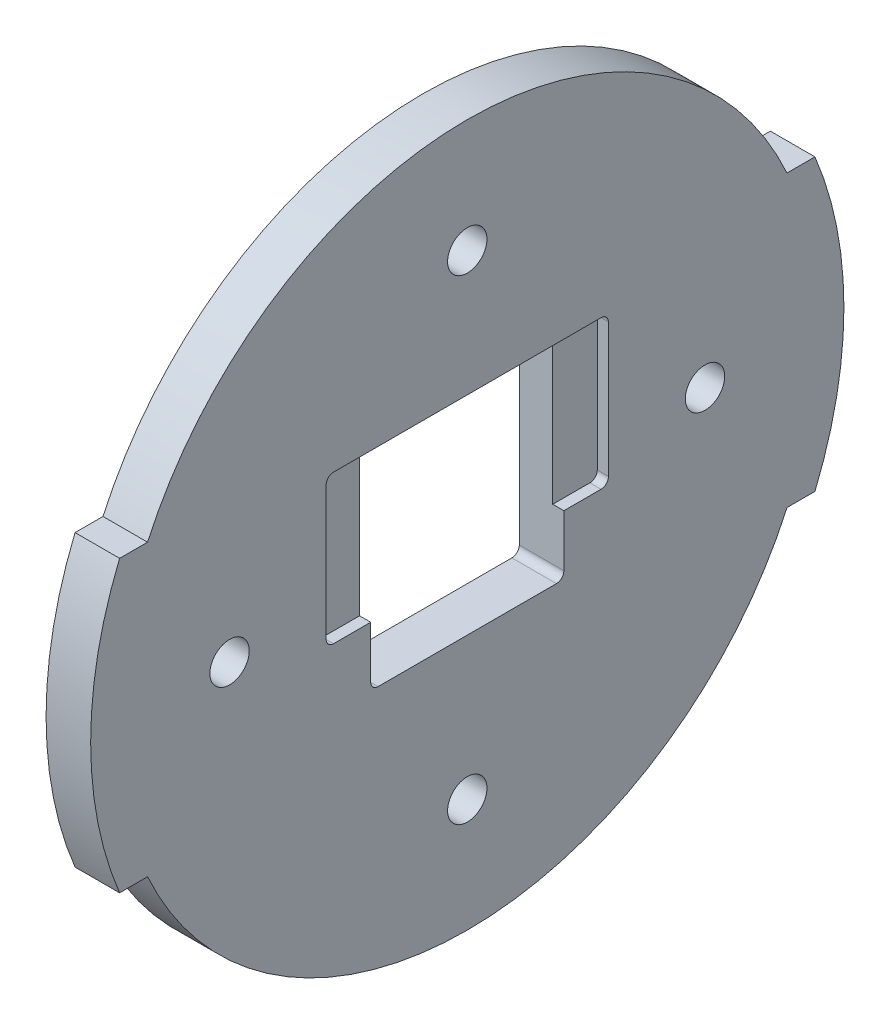
SolidWorks part; units mm, degrees
material "Perspex (TM) GS Acrylic Cast Sheet"
ref_plane "Front Plane" through (0, 0, 0) normal (0, 0, 1) x (1, 0, 0)
ref_plane "Top Plane" through (0, 0, 0) normal (0, 1, 0) x (1, 0, 0)
ref_plane "Right Plane" through (0, 0, 0) normal (1, 0, 0) x (0, 0, -1)
sketch "Sketch1" plane through (0, 0, 0) normal (1, 0, 0) x (0, 0, -1)
  line L0 (-46.8, 19.5) -> (-43.0385, 19.5)
  line L3 (-46.8, -19.5) -> (-43.0385, -19.5)
  line L4 (46.8, -19.5) -> (43.0385, -19.5)
  line L5 (46.8, 19.5) -> (43.0385, 19.5)
  arc A0 (-43.0385, -19.5) -> (43.0385, -19.5) centre (0, 0) ccw
  arc A1 (-46.8, 19.5) -> (-46.8, -19.5) centre (0, 0) ccw
  arc A2 (46.8, -19.5) -> (46.8, 19.5) centre (0, 0) ccw
  arc A3 (43.0385, 19.5) -> (-43.0385, 19.5) centre (0, 0) ccw
  dimension "D1" = 101.4
  dimension "D2" = 94.5
  dimension "D3" = 19.5
  dimension "D4" = 39
  dimension "D5" = 19.5
  dimension "D6" = 39
extrude "Boss-Extrude1" add sketch "Sketch1" along normal blind 6
sketch "Sketch2" plane through (6, 0, 0) normal (1, 0, 0) x (0, 0, -1)
  line L0 (12, -12.85) -> (-12, -12.85)
  line L1 (13, -3.85) -> (13, -11.85)
  line L2 (12, -11.85) -> (-12, -11.85)
  line L3 (-13, -11.85) -> (-13, -3.85)
  line L4 (-13, -3.85) -> (-13, 14.15)
  line L5 (13, -3.85) -> (13, 14.15)
  line L6 (12, 15.15) -> (-12, 15.15)
  line L7 (12, -12.85) -> (-12, -12.85) construction
  arc A0 (-13, -11.85) -> (-12, -12.85) centre (-12, -11.85) ccw
  arc A1 (13, -11.85) -> (12, -12.85) centre (12, -11.85) cw
  arc A4 (12, -11.85) -> (13, -10.85) centre (12, -10.85) ccw
  arc A5 (-13, -10.85) -> (-12, -11.85) centre (-12, -10.85) ccw
  arc A8 (-13, 14.15) -> (-12, 15.15) centre (-12, 14.15) cw
  arc A9 (13, 14.15) -> (12, 15.15) centre (12, 14.15) ccw
  point P26 (13, 15.15)
  dimension "D2" = 1
  dimension "D4" = 1
  dimension "D1" = 19
  dimension "D3" = 1
extrude "Cut-Extrude1" cut sketch "Sketch2" against normal blind 20 contours L5 A9 L6 A8 L4 L3 A5 L2 A4 L1 | A5 L3 A0 L0 A1 L1 A4 L2
sketch "Sketch3" plane through (6, 0, 0) normal (1, 0, 0) x (0, 0, -1)
  line L0 (0, 0) -> (-33.4108, 33.4108)
  line L1 (-33.4108, 33.4108) -> (33.4108, -33.4108)
  line L2 (0, 0) -> (33.4108, 33.4108)
  line L3 (0, 0) -> (-33.4108, -33.4108)
  circle A0 centre (0, 0) radius 47.25 construction
ref_plane "Plane1" through (0, 33.4108, 33.4108) normal (0, 0.7071, 0.7071) x (-1, 0, 0)
ref_plane "Plane2" through (0, -33.4108, 33.4108) normal (0, -0.7071, 0.7071) x (-1, 0, 0)
ref_plane "Plane3" through (0, 33.4108, -33.4108) normal (0, 0.7071, -0.7071) x (-1, 0, 0)
ref_plane "Plane4" through (0, -33.4108, -33.4108) normal (0, -0.7071, -0.7071) x (-1, 0, 0)
hole_wizard "M5 Clearance Hole1" positions "Sketch15" profile "Sketch14" hole size "M5" standard "ISO"
sketch "Sketch15" plane through (0, 0, 0) normal (-1, 0, 0) x (0, 0, 1)
  point P0 (-32, 0)
  point P8 (0, 32)
  point P9 (32, 0)
  point P10 (0, -32)
  dimension "D2" = 4
sketch "Sketch14" plane through (0, 0, -32) normal (0, 1, 0) x (0, 0, 1)
  line L0 (0, 0) -> (0, 16.5923)
  line L1 (0, 16.5923) -> (2.65, 15)
  line L2 (2.65, 15) -> (2.65, 0)
  line L5 (2.65, 0) -> (0, 0)
  line L10 (0, 16.5923) -> (-2.65, 15) construction
  line L11 (0, -6.35) -> (0, 107.95) construction
  dimension "Hole Dia." = 5.3
  dimension "Hole Depth" = 15
  dimension "Drill Angle" = 118
sketch "Sketch16" plane through (6, 0, 0) normal (1, 0, 0) x (0, 0, -1)
  line L0 (12, 15.15) -> (-12, 15.15) construction
  line L1 (19, 15.15) -> (-19, 15.15)
  line L2 (0, 15.15) -> (0, -4.85)
  line L3 (19, -4.85) -> (-19, -4.85)
  line L4 (-19, 15.15) -> (-19, -4.85)
  line L5 (19, 15.15) -> (19, -4.85)
  line M5 (13, 14.15) -> (13, -11.85)
  line M9 (-13, -11.85) -> (-13, 14.15)
  arc M10 (-13, 14.15) -> (-12, 15.15) centre (-12, 14.15) cw
  line M11 (-12, 15.15) -> (12, 15.15)
  arc M12 (12, 15.15) -> (13, 14.15) centre (12, 14.15) cw
  dimension "D1" = 20
  dimension "D2" = 19
extrude "Cut-Extrude2" cut sketch "Sketch16" against normal blind 1.5 contours L1 L4 L3 M9 M10 | L3 L2 M11 M10 M9 | L3 L1 L2 M5 M12 | L5 L1 L3 M12 M5
fillet "Fillet1" radius 1 4 edges at (5.25, -4.85, 19) (5.25, -4.85, -19) (5.25, 15.15, -19) (5.25, 15.15, 19)
